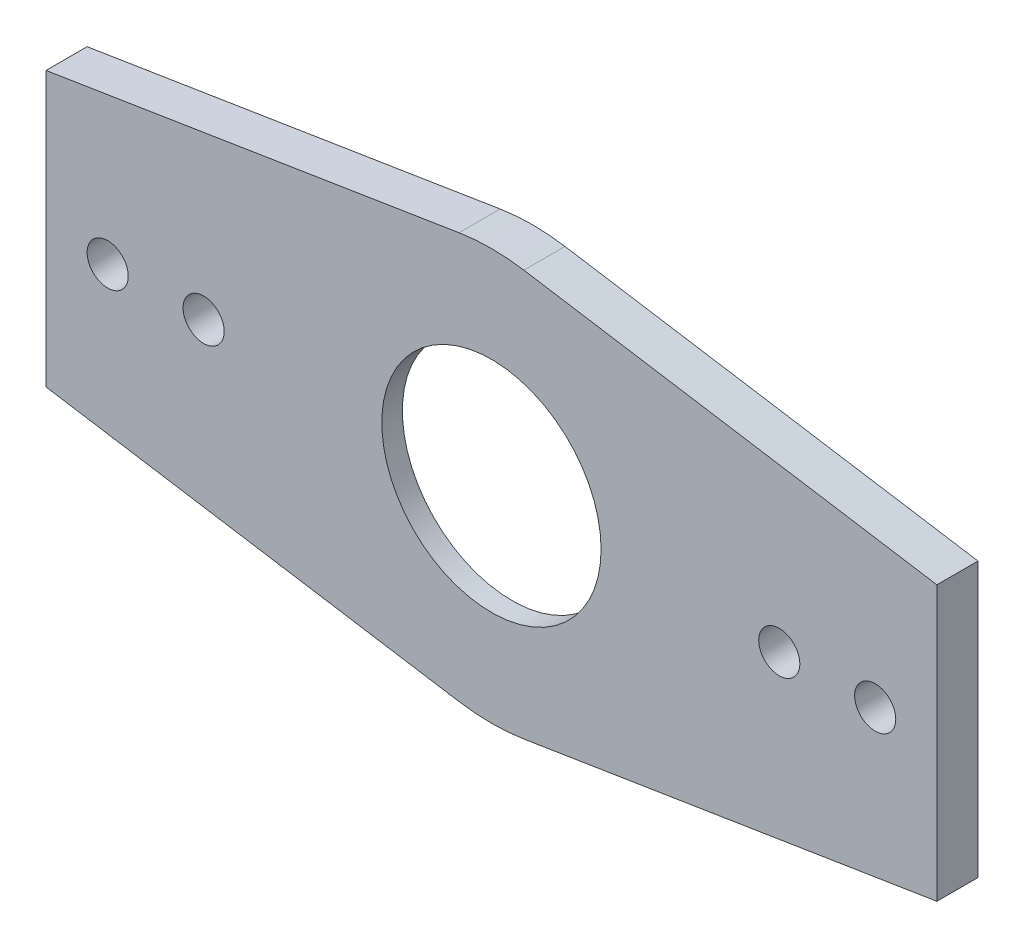
SolidWorks part; units mm, degrees
material "6063-O"
ref_plane "Front Plane" through (0, 0, 0) normal (0, 0, 1) x (1, 0, 0)
ref_plane "Top Plane" through (0, 0, 0) normal (0, 1, 0) x (1, 0, 0)
ref_plane "Right Plane" through (0, 0, 0) normal (1, 0, 0) x (0, 0, -1)
sketch "Sketch1" plane through (0, 0, 0) normal (0, 0, 1) x (1, 0, 0)
  line L0 (-65, 0) -> (65, 0) construction
  line L5 (-65, 20) -> (-65, -20)
  line L6 (-65, 20) -> (-4.7309, 29.6246)
  line L7 (-65, -20) -> (-4.7309, -29.6246)
  line L8 (0, 0) -> (0, 30) construction
  line L9 (65, -20) -> (4.7309, -29.6246)
  line L10 (65, 20) -> (65, -20)
  line L11 (65, 20) -> (4.7309, 29.6246)
  line L12 (-33, 25.1102) -> (-33, -25.1102) construction
  circle A0 centre (0, 0) radius 23.5 construction
  arc A1 (-4.7309, -29.6246) -> (4.7309, -29.6246) centre (0, 0) ccw
  circle A2 centre (56, 0) radius 3
  circle A3 centre (42, 0) radius 3
  arc A4 (4.7309, 29.6246) -> (-4.7309, 29.6246) centre (0, 0) ccw
  circle A5 centre (-56, 0) radius 3
  circle A6 centre (-42, 0) radius 3
  circle A7 centre (0, 0) radius 16
  point P7 (0, 0)
  point P10 (-65, 0)
  dimension "D1" = 47
  dimension "D2" = 60
  dimension "D5" = 6
  dimension "D7" = 6
  dimension "D9" = 32
  dimension "D3" = 130
  dimension "D4" = 40
  dimension "D6" = 9
  dimension "D8" = 14
  dimension "D10" = 33
  dimension "D11" = 84
extrude "Boss-Extrude1" add sketch "Sketch1" along normal blind 3
sketch "Sketch3" plane through (0, 0, 0) normal (0, 0, -1) x (-1, 0, 0)
  circle A0 centre (0, 0) radius 21
  circle A1 centre (0, 0) radius 30
  dimension "D1" = 42
  dimension "D2" = 60
extrude "Boss-Extrude3" add sketch "Sketch3" along normal blind 3.5
sketch "Sketch4" plane through (0, 0, 0) normal (0, 0, -1) x (-1, 0, 0)
  line L3 (4.7309, -29.6246) -> (65, -20)
  line L4 (65, -20) -> (65, 20)
  line L5 (65, 20) -> (4.7309, 29.6246)
  line L6 (4.7309, -29.6246) -> (65, -20)
  line L7 (65, -20) -> (65, 20)
  line L8 (65, 20) -> (4.7309, 29.6246)
  line L9 (-4.7309, 29.6246) -> (-65, 20)
  line L10 (-65, 20) -> (-65, -20)
  line L11 (-65, -20) -> (-4.7309, -29.6246)
  line L12 (-4.7309, 29.6246) -> (-65, 20)
  line L13 (-65, 20) -> (-65, -20)
  line L14 (-65, -20) -> (-4.7309, -29.6246)
  circle A0 centre (56, 0) radius 3 construction
  arc A1 (4.7309, -29.6246) -> (4.7309, 29.6246) centre (0, 0) ccw
  arc A2 (4.7309, -29.6246) -> (4.7309, 29.6246) centre (0, 0) ccw
  arc A3 (-4.7309, 29.6246) -> (-4.7309, -29.6246) centre (0, 0) ccw
  arc A4 (-4.7309, 29.6246) -> (-4.7309, -29.6246) centre (0, 0) ccw
  circle A5 centre (42, 0) radius 3 construction
  circle A6 centre (-42, 0) radius 3 construction
  circle A7 centre (-56, 0) radius 3 construction
  circle A8 centre (56, 0) radius 3
  circle A9 centre (42, 0) radius 3
  circle A10 centre (-42, 0) radius 3
  circle A11 centre (-56, 0) radius 3
  dimension "D1" = 0
  dimension "D2" = 0
extrude "Boss-Extrude4" add sketch "Sketch4" along normal blind 3.5
sketch "Sketch5" plane through (0, 0, -3.5) normal (0, 0, -1) x (-1, 0, 0)
  line L6 (-4.7309, 29.6246) -> (-65, 20)
  line L7 (-65, 20) -> (-65, -20)
  line L8 (-65, -20) -> (-4.7309, -29.6246)
  line L9 (4.7309, -29.6246) -> (65, -20)
  line L10 (65, -20) -> (65, 20)
  line L11 (65, 20) -> (4.7309, 29.6246)
  line L12 (-4.7309, 29.6246) -> (-65, 20)
  line L13 (-65, 20) -> (-65, -20)
  line L14 (-65, -20) -> (-4.7309, -29.6246)
  line L15 (4.7309, -29.6246) -> (65, -20)
  line L16 (65, -20) -> (65, 20)
  line L17 (65, 20) -> (4.7309, 29.6246)
  circle A0 centre (56, 0) radius 3 construction
  circle A1 centre (42, 0) radius 3 construction
  arc A2 (4.7309, 29.6246) -> (-4.7309, 29.6246) centre (0, 0) ccw
  arc A3 (-4.7309, -29.6246) -> (4.7309, -29.6246) centre (0, 0) ccw
  arc A4 (4.7309, 29.6246) -> (-4.7309, 29.6246) centre (0, 0) ccw
  arc A5 (-4.7309, -29.6246) -> (4.7309, -29.6246) centre (0, 0) ccw
  circle A6 centre (0, 0) radius 21 construction
  circle A7 centre (-42, 0) radius 3 construction
  circle A8 centre (-56, 0) radius 3 construction
  circle A9 centre (56, 0) radius 3
  circle A10 centre (42, 0) radius 3
  circle A11 centre (0, 0) radius 21
  circle A12 centre (-42, 0) radius 3
  circle A13 centre (-56, 0) radius 3
  dimension "D1" = 0
extrude "Cut-Extrude1" cut sketch "Sketch5" against normal blind 0.5
